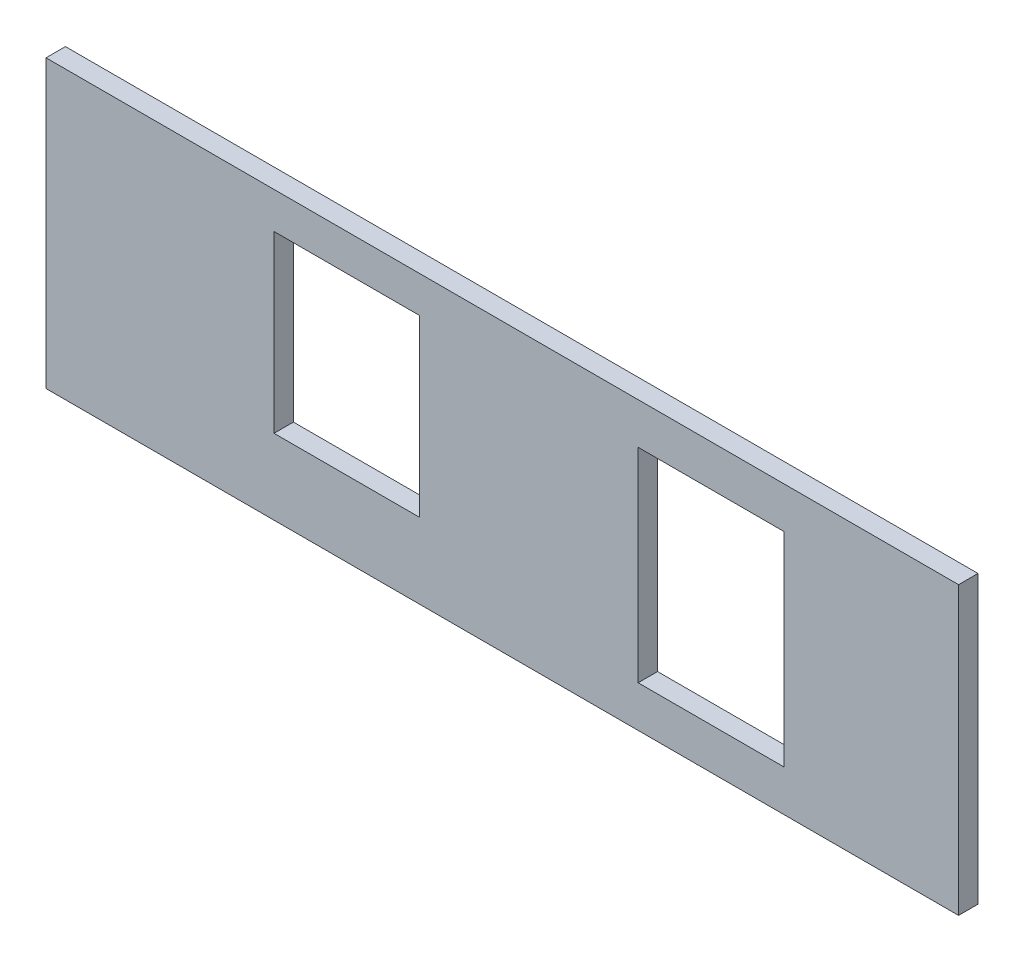
SolidWorks part; units mm, degrees
ref_plane "Front Plane" through (0, 0, 0) normal (0, 0, 1) x (1, 0, 0)
ref_plane "Top Plane" through (0, 0, 0) normal (0, 1, 0) x (1, 0, 0)
ref_plane "Right Plane" through (0, 0, 0) normal (1, 0, 0) x (0, 0, -1)
sketch "Croquis1" plane through (0, 0, 0) normal (0, 0, 1) x (1, 0, 0)
  line L0 (520.6747, 450) -> (524.2446, 178.6032) construction
  line L1 (-600, -475) -> (600, -475)
  line L2 (-600, -475) -> (-600, 475)
  line L3 (-600, 475) -> (600, 475)
  line L4 (600, -475) -> (600, 475)
  point P4 (600, 0)
  point P6 (0, -475)
  dimension "D1" = 950
  dimension "D2" = 1200
extrude "Saliente-Extruir1" add sketch "Croquis1" along normal blind 20
sketch "Croquis2" plane through (0, 0, 20) normal (0, 0, 1) x (1, 0, 0)
  line L1 (-275, 435) -> (-125, 435)
  line L2 (-275, 435) -> (-275, 255)
  line L3 (-275, 255) -> (-125, 255)
  line L4 (-125, 435) -> (-125, 255)
  line L5 (-600, 475) -> (-600, -475) construction
  line L6 (600, 475) -> (-600, 475) construction
  dimension "D1" = 150
  dimension "D2" = 180
  dimension "D3" = 40
  dimension "D4" = 325
extrude "Cortar-Extruir1" cut sketch "Croquis2" against normal blind 20
sketch "Croquis3" plane through (0, 0, 0) normal (0, 0, -1) x (-1, 0, 0)
  line L5 (-600, -475) -> (-600, 475) construction
  line L6 (600, -475) -> (-600, -475) construction
  line L7 (-375, -415) -> (275, -415)
  line L8 (-375, -415) -> (-375, 85)
  line L9 (-375, 85) -> (275, 85)
  line L10 (275, -415) -> (275, 85)
  dimension "D4" = 500
  dimension "D5" = 650
  dimension "D6" = 225
  dimension "D7" = 60
extrude "Cortar-Extruir2" cut sketch "Croquis3" against normal blind 20
ref_plane "Plano1" through (600, -475, 0) normal (0, 1, 0) x (1, 0, 0)
sketch "Croquis6" plane through (0, 0, 0) normal (0, 0, -1) x (-1, 0, 0)
  line L0 (600, 175) -> (-600, 175)
  line L1 (600, 475) -> (600, -475) construction
  line L2 (-600, -475) -> (-600, 475) construction
  line L3 (-600, 175) -> (-633.2846, 175)
  line L4 (-633.2846, 175) -> (-633.2846, -516.1561)
  line L5 (-633.2846, -516.1561) -> (737.0255, -516.1561)
  line L6 (737.0255, -516.1561) -> (737.0255, 175)
  line L7 (737.0255, 175) -> (600, 175)
  line L8 (275, 85) -> (-375, 85) construction
  dimension "D1" = 90
extrude "Cortar-Extruir4" cut sketch "Croquis6" against normal blind 50
sketch "Croquis7" plane through (0, 0, 0) normal (0, 0, -1) x (-1, 0, 0)
  line L0 (-600, 175) -> (-600, 475) construction
  line L1 (-250, 220) -> (-100, 220)
  line L2 (-250, 220) -> (-250, 430)
  line L3 (-250, 430) -> (-100, 430)
  line L4 (-100, 220) -> (-100, 430)
  line L5 (600, 175) -> (-600, 175) construction
  dimension "D1" = 210
  dimension "D2" = 150
  dimension "D3" = 350
  dimension "D4" = 45
extrude "Cortar-Extruir5" cut sketch "Croquis7" against normal blind 50
sketch "Croquis8" plane through (0, 0, 0) normal (0, 0, -1) x (-1, 0, 0)
  line L0 (-600, 475) -> (600, 475) construction
  line L1 (694.0179, 962.0694) -> (-820.7334, 962.0694)
  line L2 (694.0179, 962.0694) -> (694.0179, 472.5)
  line L3 (694.0179, 472.5) -> (-820.7334, 472.5)
  line L4 (-820.7334, 962.0694) -> (-820.7334, 472.5)
  dimension "D1" = 2.5
extrude "Cortar-Extruir6" cut sketch "Croquis8" against normal blind 30
sketch "Croquis9" plane through (0, 0, 0) normal (0, 0, -1) x (-1, 0, 0)
  line L0 (600, 175) -> (-600, 175) construction
  line L1 (773.0481, -302.2578) -> (-955.506, -302.2578)
  line L2 (773.0481, -302.2578) -> (773.0481, 177.5)
  line L3 (773.0481, 177.5) -> (-955.506, 177.5)
  line L4 (-955.506, -302.2578) -> (-955.506, 177.5)
  dimension "D1" = 2.5
extrude "Cortar-Extruir7" cut sketch "Croquis9" against normal blind 30
sketch "Croquis10" plane through (0, 0, 0) normal (0, 0, -1) x (-1, 0, 0)
  line L0 (-600, 472.5) -> (600, 472.5) construction
  line L1 (600, 177.5) -> (509.8, 177.5)
  line L2 (600, 177.5) -> (600, 472.5)
  line L3 (600, 472.5) -> (509.8, 472.5)
  line L4 (509.8, 177.5) -> (509.8, 472.5)
  line L6 (-600, 177.5) -> (-430, 177.5)
  line L7 (-600, 177.5) -> (-600, 472.5)
  line L8 (-600, 472.5) -> (-430, 472.5)
  line L9 (-430, 177.5) -> (-430, 472.5)
  dimension "D1" = 90.2
  dimension "D2" = 170
extrude "Cortar-Extruir8" cut sketch "Croquis10" against normal blind 30
